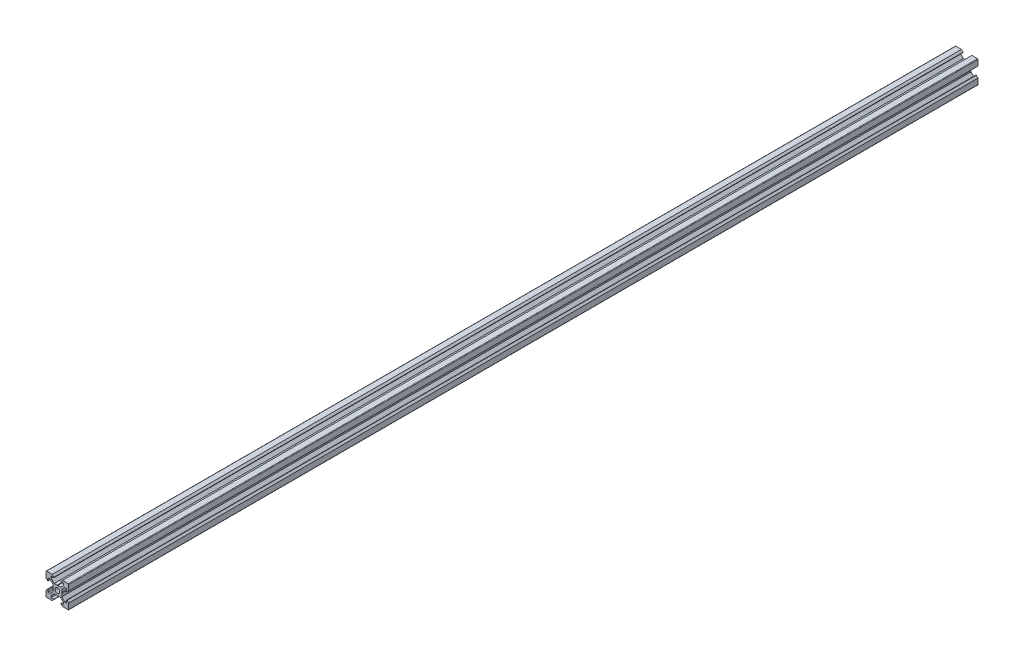
SolidWorks part; units mm, degrees
ref_plane "Front Plane" through (0, 0, 0) normal (0, 0, 1) x (1, 0, 0)
ref_plane "Top Plane" through (0, 0, 0) normal (0, 1, 0) x (1, 0, 0)
ref_plane "Right Plane" through (0, 0, 0) normal (1, 0, 0) x (0, 0, -1)
sketch "Sketch1" plane through (0, 0, 0) normal (0, 0, 1) x (1, 0, 0)
  line B0 (3.69, 0) -> (3.9, -0.21)
  line B1 (3.9, -0.21) -> (3.9, -2.8393)
  line B2 (3.9, -2.8393) -> (6.5607, -5.5)
  line B3 (6.5607, -5.5) -> (8.2, -5.5)
  line B4 (8.2, -5.5) -> (8.2, -3.125)
  line B5 (8.2, -3.125) -> (8.545, -3.125)
  line B6 (8.545, -3.125) -> (10, -4.58)
  line B7 (10, -9.5) -> (10, -4.58)
  arc B8 (9.5, -10) -> (10, -9.5) centre (9.5, -9.5) ccw
  line B9 (9.5, -10) -> (4.58, -10)
  line B10 (3.125, -8.545) -> (4.58, -10)
  line B11 (3.125, -8.2) -> (3.125, -8.545)
  line B12 (5.5, -8.2) -> (3.125, -8.2)
  line B13 (5.5, -6.5607) -> (5.5, -8.2)
  line B14 (2.8393, -3.9) -> (5.5, -6.5607)
  line B15 (0.21, -3.9) -> (2.8393, -3.9)
  line B16 (0, -3.69) -> (0.21, -3.9)
  line B17 (0, -3.69) -> (-0.21, -3.9)
  line B18 (-0.21, -3.9) -> (-2.8393, -3.9)
  line B19 (-2.8393, -3.9) -> (-5.5, -6.5607)
  line B20 (-5.5, -6.5607) -> (-5.5, -8.2)
  line B21 (-5.5, -8.2) -> (-3.125, -8.2)
  line B22 (-3.125, -8.2) -> (-3.125, -8.545)
  line B23 (-3.125, -8.545) -> (-4.58, -10)
  line B24 (-4.58, -10) -> (-9.5, -10)
  arc B25 (-10, -9.5) -> (-9.5, -10) centre (-9.5, -9.5) ccw
  line B26 (-10, -9.5) -> (-10, -4.58)
  line B27 (-8.545, -3.125) -> (-10, -4.58)
  line B28 (-8.2, -3.125) -> (-8.545, -3.125)
  line B29 (-8.2, -5.5) -> (-8.2, -3.125)
  line B30 (-6.5607, -5.5) -> (-8.2, -5.5)
  line B31 (-3.9, -2.8393) -> (-6.5607, -5.5)
  line B32 (-3.9, -0.21) -> (-3.9, -2.8393)
  line B33 (-3.69, 0) -> (-3.9, -0.21)
  line B34 (-3.69, 0) -> (-3.9, 0.21)
  line B35 (-3.9, 0.21) -> (-3.9, 2.8393)
  line B36 (-3.9, 2.8393) -> (-6.5607, 5.5)
  line B37 (-6.5607, 5.5) -> (-8.2, 5.5)
  line B38 (-8.2, 5.5) -> (-8.2, 3.125)
  line B39 (-8.2, 3.125) -> (-8.545, 3.125)
  line B40 (-8.545, 3.125) -> (-10, 4.58)
  line B41 (-10, 4.58) -> (-10, 9.5)
  arc B42 (-9.5, 10) -> (-10, 9.5) centre (-9.5, 9.5) ccw
  line B43 (-4.58, 10) -> (-9.5, 10)
  line B44 (-3.125, 8.545) -> (-4.58, 10)
  line B45 (-3.125, 8.2) -> (-3.125, 8.545)
  line B46 (-5.5, 8.2) -> (-3.125, 8.2)
  line B47 (-5.5, 6.5607) -> (-5.5, 8.2)
  line B48 (-2.8393, 3.9) -> (-5.5, 6.5607)
  line B49 (-0.21, 3.9) -> (-2.8393, 3.9)
  line B50 (0, 3.69) -> (-0.21, 3.9)
  line B51 (0, 3.69) -> (0.21, 3.9)
  line B52 (0.21, 3.9) -> (2.8393, 3.9)
  line B53 (2.8393, 3.9) -> (5.5, 6.5607)
  line B54 (5.5, 6.5607) -> (5.5, 8.2)
  line B55 (5.5, 8.2) -> (3.125, 8.2)
  line B56 (3.125, 8.2) -> (3.125, 8.545)
  line B57 (3.125, 8.545) -> (4.58, 10)
  line B58 (9.5, 10) -> (4.58, 10)
  arc B59 (10, 9.5) -> (9.5, 10) centre (9.5, 9.5) ccw
  line B60 (10, 4.58) -> (10, 9.5)
  line B61 (8.545, 3.125) -> (10, 4.58)
  line B62 (8.2, 3.125) -> (8.545, 3.125)
  line B63 (8.2, 5.5) -> (8.2, 3.125)
  line B64 (6.5607, 5.5) -> (8.2, 5.5)
  line B65 (3.9, 2.8393) -> (6.5607, 5.5)
  line B66 (3.9, 0.21) -> (3.9, 2.8393)
  line B67 (3.69, 0) -> (3.9, 0.21)
  circle B68 centre (0, 0) radius 2.1
sketch_block_instance "2020 - V-Slot-1"
sketch_block "2020 - V-Slot"
extrude "Boss-Extrude1" add sketch "Sketch1" along normal blind 800
